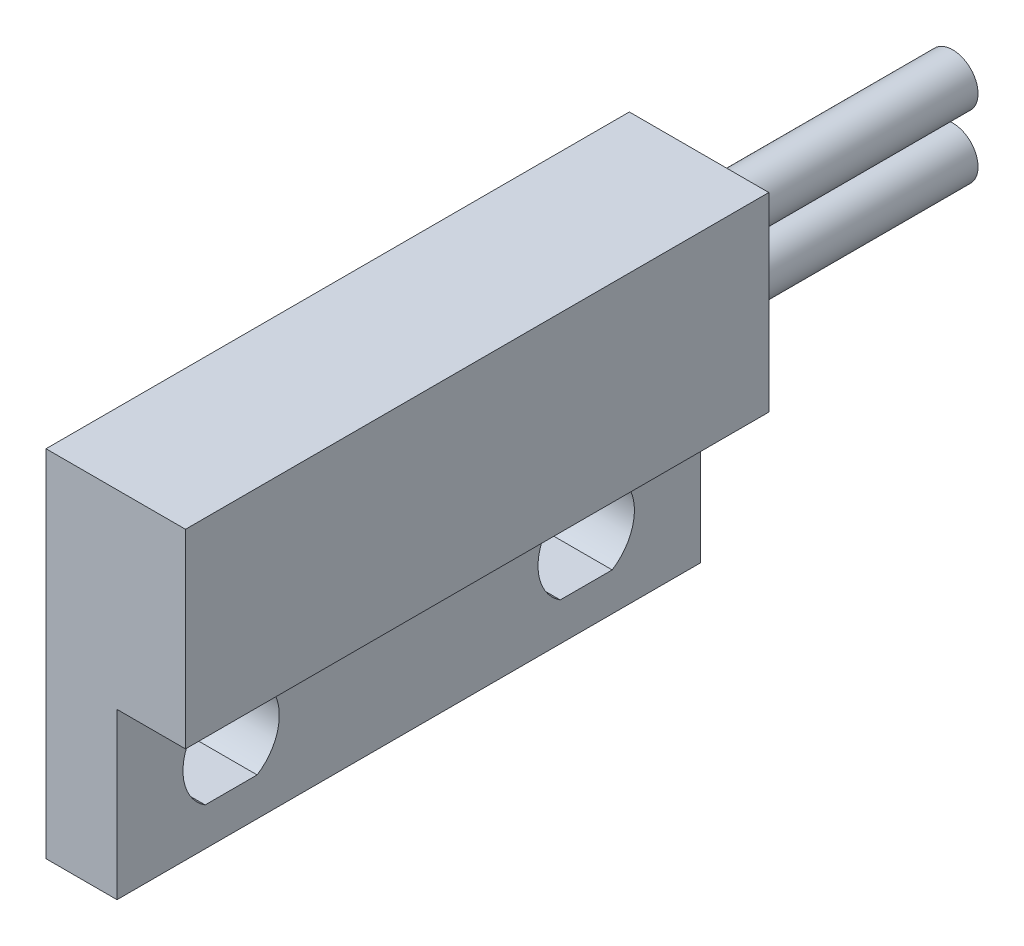
SolidWorks part; units mm, degrees
ref_plane "Płaszczyzna przednia" through (0, 0, 0) normal (0, 0, 1) x (1, 0, 0)
ref_plane "Płaszczyzna górna" through (0, 0, 0) normal (0, 1, 0) x (1, 0, 0)
ref_plane "Płaszczyzna prawa" through (0, 0, 0) normal (1, 0, 0) x (0, 0, -1)
sketch "Szkic1" plane through (0, 0, 0) normal (0, 0, 1) x (1, 0, 0)
  line L0 (0, 0) -> (0, 14)
  line L1 (0, 14) -> (5.5, 14)
  line L2 (5.5, 14) -> (5.5, 6.5)
  line L3 (5.5, 6.5) -> (2.8, 6.5)
  line L4 (2.8, 6.5) -> (2.8, 0)
  line L5 (2.8, 0) -> (0, 0)
  dimension "D1" = 5.5
  dimension "D2" = 7.5
  dimension "D3" = 14
  dimension "D4" = 2.8
extrude "Dodanie-wyciągnięcie1" add sketch "Szkic1" against normal mid plane 23
sketch "Szkic2" plane through (0, 0, -11.5) normal (0, 0, -1) x (-1, 0, 0)
  line L0 (-2.75, 14) -> (-2.75, 11.5) construction
  line L1 (-5.5, 14) -> (0, 14) construction
  line L2 (-2.75, 11.5) -> (-2.75, 9) construction
  line L3 (-2.75, 9) -> (-2.75, 6.5) construction
  line L4 (-2.8, 6.5) -> (-5.5, 6.5) construction
  line L5 (-5.5, 6.5) -> (-5.5, 14) construction
  circle A0 centre (-2.75, 11.5) radius 1
  circle A1 centre (-2.75, 9) radius 1
  point P9 (-2.75, 10.25)
  point P12 (-5.5, 10.25)
  dimension "D1" = 2
  dimension "D2" = 2.5
extrude "Dodanie-wyciągnięcie2" add sketch "Szkic2" along normal blind 10
sketch "Szkic3" plane through (2.8, 0, 0) normal (1, 0, 0) x (0, 0, -1)
  line L0 (-11.5, 3.1) -> (-7, 3.1) construction
  line L1 (-8.0247, 1.5) -> (-5.9753, 1.5)
  line L2 (-8.0247, 1.5) -> (-8.0247, 4.7) construction
  line L3 (-8.0247, 4.7) -> (-5.9753, 4.7)
  line L4 (-5.9753, 1.5) -> (-5.9753, 4.7) construction
  line L5 (-8.0247, 1.5) -> (-5.9753, 4.7) construction
  line L6 (-8.0247, 4.7) -> (-5.9753, 1.5) construction
  line L7 (8.0247, 1.5) -> (5.9753, 1.5)
  line L8 (8.0247, 1.5) -> (8.0247, 4.7) construction
  line L9 (8.0247, 4.7) -> (5.9753, 4.7)
  line L10 (5.9753, 1.5) -> (5.9753, 4.7) construction
  line L11 (8.0247, 1.5) -> (5.9753, 4.7) construction
  line L12 (8.0247, 4.7) -> (5.9753, 1.5) construction
  line L13 (-11.5, 0) -> (-11.5, 6.5) construction
  line L14 (-7, 3.1) -> (7, 3.1) construction
  line L15 (7, 3.1) -> (11.5, 3.1) construction
  line L16 (11.5, 0) -> (11.5, 6.5) construction
  line L17 (11.5, 0) -> (-11.5, 0) construction
  arc A0 (-8.0247, 4.7) -> (-8.0247, 1.5) centre (-7, 3.1) ccw
  arc A1 (5.9753, 4.7) -> (5.9753, 1.5) centre (7, 3.1) ccw
  arc A2 (8.0247, 1.5) -> (8.0247, 4.7) centre (7, 3.1) ccw
  arc A3 (-5.9753, 1.5) -> (-5.9753, 4.7) centre (-7, 3.1) ccw
  point P3 (-8.9, 3.1)
  point P17 (-5.1, 3.1)
  dimension "D2" = 3.8
  dimension "D1" = 14
  dimension "D3" = 1.5
  dimension "D4" = 3.2
extrude "Wytnij-wyciągnięcie1" cut sketch "Szkic3" against normal blind 10
